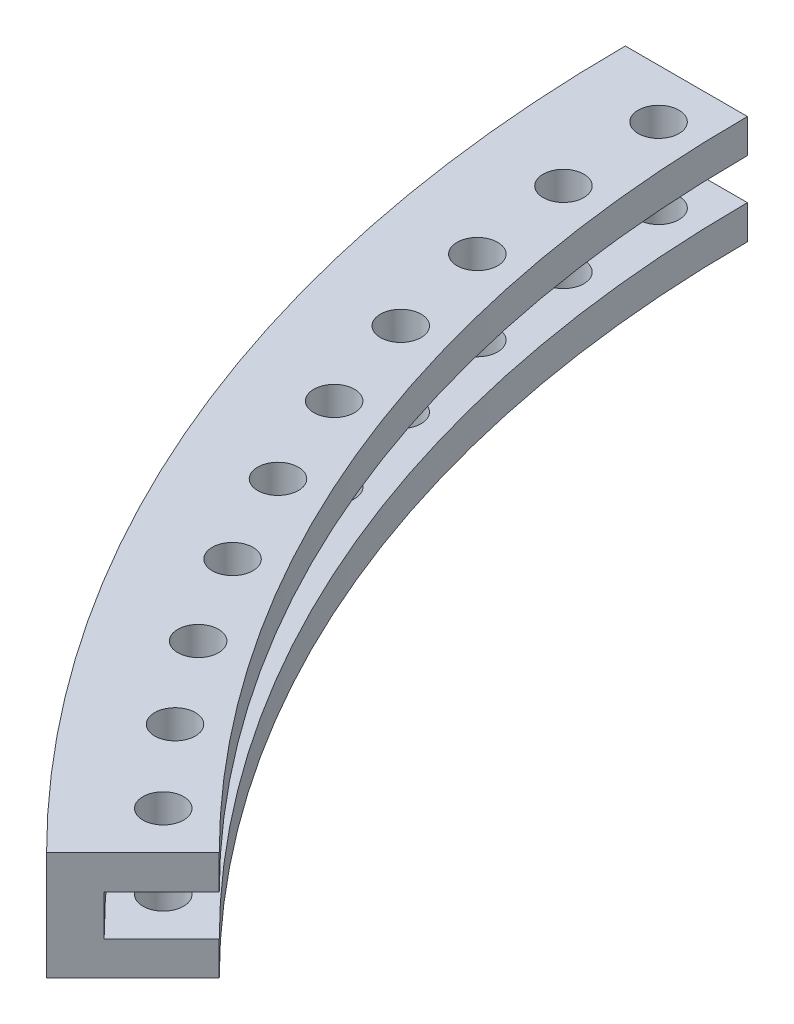
SolidWorks part; units mm, degrees
ref_plane "Front Plane" through (0, 0, 0) normal (0, 0, 1) x (1, 0, 0)
ref_plane "Top Plane" through (0, 0, 0) normal (0, 1, 0) x (1, 0, 0)
ref_plane "Right Plane" through (0, 0, 0) normal (1, 0, 0) x (0, 0, -1)
ref_axis "Axe1" through (0, -55, 0) along (0, 1, 0)
sketch "Esquisse2" plane through (0, 0, 0) normal (0, 0, 1) x (1, 0, 0)
  line L0 (-103, 4) -> (-103, -4)
  line L1 (-103, -4) -> (-94, -4)
  line L2 (-94, -4) -> (-94, -1.5)
  line L3 (-94, -1.5) -> (-100, -1.5)
  line L4 (-100, -1.5) -> (-100, 1.5)
  line L5 (-100, 1.5) -> (-94, 1.5)
  line L6 (-94, 1.5) -> (-94, 4)
  line L7 (-94, 4) -> (-103, 4)
  line L9 (0, -55) -> (0, 55) construction
  point P2 (-100, 0)
  dimension "D1" = 100
  dimension "D2" = 3
  dimension "D3" = 3
  dimension "D4" = 8
  dimension "D5" = 6
  dimension "D6" = 94
revolve "Révolution1" add sketch "Esquisse2" angle 45 about axis through (0, -55, 0) along (0, 1, 0)
sketch "Esquisse3" plane through (0, 4, 0) normal (0, 1, 0) x (1, 0, 0)
  line L0 (-66.468, -66.468) -> (-72.832, -72.832) construction
  circle A0 centre (-71.3594, -65.7026) radius 1.5
  dimension "D1" = 3
  dimension "D2" = 97
  dimension "D3" = 4
extrude "Enlèv. mat.-Extru.1" cut sketch "Esquisse3" against normal through all
pattern_circular "Répétition circulaire1" count 10 every 4.5 about axis through (0, 0, 0) along (0, 1, 0) of "Enlèv. mat.-Extru.1"
